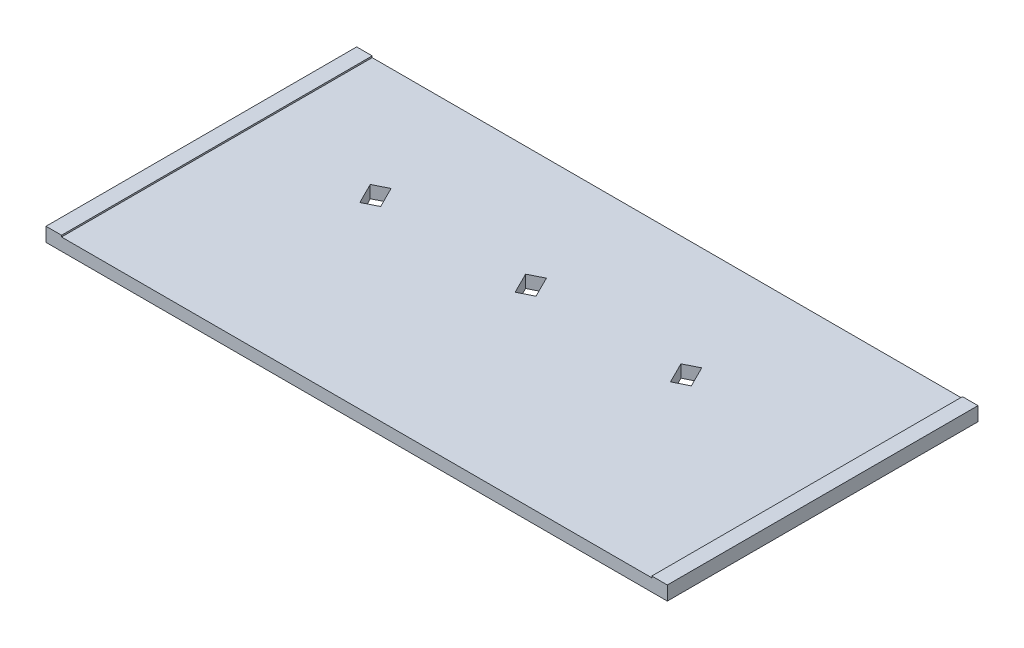
SolidWorks part; units mm, degrees
ref_plane "Front Plane" through (0, 0, 0) normal (0, 0, 1) x (1, 0, 0)
ref_plane "Top Plane" through (0, 0, 0) normal (0, 1, 0) x (1, 0, 0)
ref_plane "Right Plane" through (0, 0, 0) normal (1, 0, 0) x (0, 0, -1)
sketch "Sketch1" plane through (0, 0, 0) normal (0, 1, 0) x (1, 0, 0)
  line L1 (-50.8, -25.4) -> (50.8, -25.4)
  line L2 (-50.8, -25.4) -> (-50.8, 25.4)
  line L3 (-50.8, 25.4) -> (50.8, 25.4)
  line L4 (50.8, -25.4) -> (50.8, 25.4)
  line L5 (0, 25.4) -> (0, -25.4) construction
  line L6 (-50.8, 0) -> (50.8, 0) construction
  point P0 (0, 0)
  dimension "D1" = 50.8
  dimension "D2" = 101.6
extrude "Boss-Extrude1" add sketch "Sketch1" along normal blind 2.032
sketch "Sketch2" plane through (0, 2.032, 0) normal (0, 1, 0) x (1, 0, 0)
  line L0 (-3.3577, 3.8746) -> (-1.0859, 5.0107)
  line L1 (-3.3577, 3.8746) -> (-5.0618, 7.2822)
  line L2 (-1.0859, 5.0107) -> (-2.7901, 8.4183)
  line L3 (-5.0618, 7.2822) -> (-2.7901, 8.4183)
  line L5 (-1.2573, 0) -> (1.2573, 0) construction
  circle A0 centre (0, 0) radius 5.127 construction
  dimension "D1" = 10.254
  dimension "D3" = 3.81
  dimension "D4" = 2.54
  dimension "D2" = 63.43
extrude "Cut-Extrude1" cut sketch "Sketch2" against normal through all contours L3 L1 L0 L2
pattern_linear "LPattern1" count 2 spacing 25.4 along (-1, 0, 0) count 2 spacing 25.4 along (1, 0, 0) of "Cut-Extrude1"
sketch "Sketch4" plane through (0, 2.032, 0) normal (0, 1, 0) x (1, 0, 0)
  line L0 (-50.8, -25.4) -> (50.8, -25.4) construction
  line L1 (-50.8, 25.4) -> (-48.26, 25.4)
  line L2 (-50.8, 25.4) -> (-50.8, -25.4)
  line L3 (-50.8, -25.4) -> (-48.26, -25.4)
  line L4 (-48.26, 25.4) -> (-48.26, -25.4)
  line L6 (50.8, 25.4) -> (48.26, 25.4)
  line L7 (50.8, 25.4) -> (50.8, -25.4)
  line L8 (50.8, -25.4) -> (48.26, -25.4)
  line L9 (48.26, 25.4) -> (48.26, -25.4)
  line M10 (50.8, -25.4) -> (50.8, 25.4)
  line M11 (50.8, 25.4) -> (-50.8, 25.4)
  line M12 (-50.8, 25.4) -> (-50.8, -25.4)
  line M13 (-50.8, -25.4) -> (50.8, -25.4)
  dimension "D1" = 2.54
extrude "Boss-Extrude2" add sketch "Sketch4" along normal blind 0.254 contours L4 M11 M12 M13 | L9 M11 M13 M10
equation "\"Arrow Height\"= 1in"
equation "\"Button Height\"= 2in"
equation "\"Button Width\"= 4in"
equation "\"Haptic Diameter\"= 10mm"
equation "\"Haptic Thickness\"= 2.7mm"
equation "\"D1@Sketch1\"=\"Button Height\""
equation "\"D2@Sketch1\"=\"Button Width\""
equation "\"D1@Sketch2\"=\"Haptic Diameter\"+.01in"
equation "\"Arrow Spacing\"= 1in"
equation "\"Arrow Width\"= 0.75in"
equation "\"Haptic Wire Angle\"= 63.43"
equation "\"Haptic Wire Width\"= .1in"
equation "\"Hatic Wire Height\"= .15in"
equation "\"D2@Sketch2\"=\"Haptic Wire Angle\""
equation "\"D4@Sketch2\"=\"Haptic Wire Width\""
equation "\"D3@Sketch2\"=\"Hatic Wire Height\""
